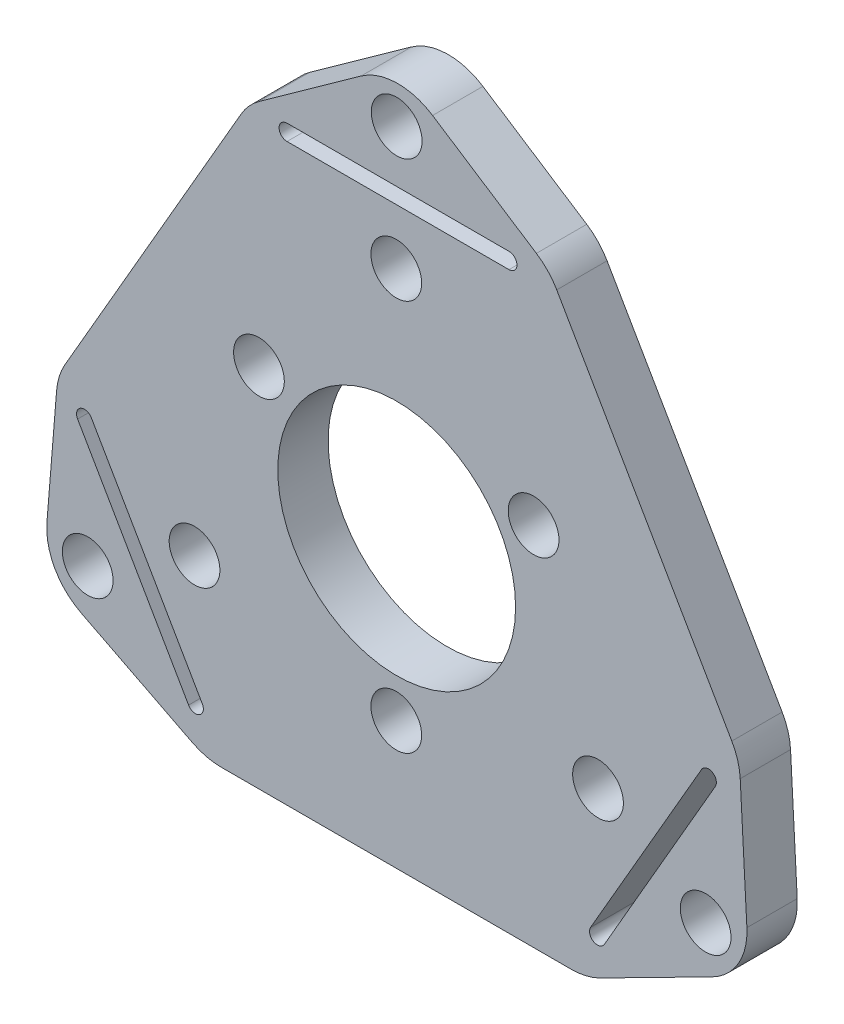
SolidWorks part; units mm, degrees
material "Acrylic (Medium-high impact)"
ref_plane "Front" through (0, 0, 0) normal (0, 0, 1) x (1, 0, 0)
ref_plane "Top" through (0, 0, 0) normal (0, 1, 0) x (1, 0, 0)
ref_plane "Right" through (0, 0, 0) normal (1, 0, 0) x (0, 0, -1)
sketch "Sketch1" plane through (0, 0, 0) normal (0, 0, 1) x (1, 0, 0)
  line L0 (31.8906, 32.2685) -> (22.25, 38.5381) construction
  line L1 (43.8906, 11.4838) -> (31.8906, 32.2685) construction
  line L2 (44.5, 0) -> (43.8906, 11.4838) construction
  line L3 (34.25, -5.2142) -> (44.5, 0) construction
  line L4 (10.25, -5.2142) -> (34.25, -5.2142) construction
  line L5 (0, 0) -> (10.25, -5.2142) construction
  line L6 (0.8998, 11.0585) -> (0, 0) construction
  line L7 (0.8998, 11.0585) -> (12.8998, 31.8431) construction
  line L8 (12.8998, 31.8431) -> (22.25, 38.5381) construction
  line L9 (31.0867, 32.7912) -> (24.5392, 37.0494)
  line L10 (43.4111, 12.3143) -> (32.3701, 31.438)
  line L11 (44.3621, 2.5977) -> (43.9414, 10.5263)
  line L12 (35.1047, -4.7794) -> (42.1814, -1.1795)
  line L13 (11.2089, -5.2142) -> (33.2911, -5.2142)
  line L14 (2.3907, -1.2162) -> (9.3953, -4.7794)
  line L15 (0.8268, 10.1619) -> (0.2175, 2.6734)
  line L16 (1.3496, 11.8375) -> (12.4674, 31.0942)
  line L17 (13.6028, 32.3465) -> (20.0297, 36.9484)
  line L18 (41.9378, 9.5622) -> (34.9378, -2.5622) construction
  line L19 (42.3708, 9.3122) -> (35.3708, -2.8122)
  line L20 (41.5048, 9.8122) -> (34.5048, -2.3122)
  line L21 (33.8665, 12.846) -> (28.0583, 22.9063) construction
  line L22 (28.0583, 2.7858) -> (33.8665, 12.846) construction
  line L23 (16.4417, 2.7858) -> (28.0583, 2.7858) construction
  line L24 (10.6335, 12.846) -> (16.4417, 2.7858) construction
  line L25 (16.4417, 22.9063) -> (10.6335, 12.846) construction
  line L26 (28.0583, 22.9063) -> (16.4417, 22.9063) construction
  line L27 (33.8665, 12.846) -> (28.0583, 22.9063) construction
  line L28 (28.0583, 2.7858) -> (33.8665, 12.846) construction
  line L29 (16.4417, 2.7858) -> (28.0583, 2.7858) construction
  line L30 (10.6335, 12.846) -> (16.4417, 2.7858) construction
  line L31 (16.4417, 22.9063) -> (10.6335, 12.846) construction
  line L32 (28.0583, 22.9063) -> (16.4417, 22.9063) construction
  line L33 (22.25, 12.846) -> (44.5, 0) construction
  line L34 (22.25, 12.846) -> (7.0114, 21.6441) construction
  line L37 (10.0175, -2.3499) -> (3.0175, 9.7744)
  line L40 (9.1515, -2.8499) -> (2.1515, 9.2744)
  line L41 (9.5845, -2.5999) -> (2.5845, 9.5244) construction
  line L42 (15.3585, 31.0381) -> (29.3585, 31.0381)
  line L43 (15.3585, 32.0381) -> (29.3585, 32.0381)
  line L44 (15.3585, 31.5381) -> (29.3585, 31.5381) construction
  line L45 (9.5263, 5.5) -> (4.2044, 2.3491) construction
  circle A0 centre (34.9737, 5.5) radius 1.5 construction
  arc A1 (9.1515, -2.8499) -> (10.0175, -2.3499) centre (9.5845, -2.5999) ccw
  arc A3 (3.0175, 9.7744) -> (2.1515, 9.2744) centre (2.5845, 9.5244) ccw
  arc A4 (15.3585, 32.0381) -> (15.3585, 31.0381) centre (15.3585, 31.5381) ccw
  arc A12 (31.0867, 32.7912) -> (32.3701, 31.438) centre (28.906, 29.438) cw
  arc A13 (43.4111, 12.3143) -> (43.9414, 10.5263) centre (39.947, 10.3143) cw
  arc A14 (44.3621, 2.5977) -> (42.1814, -1.1795) centre (40.3678, 2.3857) cw
  arc A15 (35.1047, -4.7794) -> (33.2911, -5.2142) centre (33.2911, -1.2142) cw
  arc A16 (11.2089, -5.2142) -> (9.3953, -4.7794) centre (11.2089, -1.2142) cw
  arc A17 (2.3907, -1.2162) -> (0.2175, 2.6734) centre (4.2044, 2.3491) cw
  arc A18 (0.8268, 10.1619) -> (1.3496, 11.8375) centre (4.8137, 9.8375) cw
  arc A19 (12.4674, 31.0942) -> (13.6028, 32.3465) centre (15.9315, 29.0942) cw
  arc A20 (24.5392, 37.0494) -> (20.0297, 36.9484) centre (22.3585, 33.6961) ccw
  arc A21 (42.3708, 9.3122) -> (41.5048, 9.8122) centre (41.9378, 9.5622) ccw
  arc A22 (34.5048, -2.3122) -> (35.3708, -2.8122) centre (34.9378, -2.5622) ccw
  circle A23 centre (22.25, 12.846) radius 10.0602 construction
  circle A24 centre (9.5263, 5.5) radius 1.6 construction
  circle A29 centre (34.9737, 5.5) radius 1.6 construction
  circle A31 centre (22.25, 27.5381) radius 1.6 construction
  circle A32 centre (13.5897, 17.846) radius 1.6
  circle A33 centre (9.5263, 5.5) radius 1.6
  circle A34 centre (34.9737, 5.5) radius 1.6
  circle A35 centre (30.9103, 17.846) radius 1.6
  circle A36 centre (22.25, 27.5381) radius 1.6
  circle A38 centre (22.25, 2.846) radius 1.6
  arc A39 (29.3585, 31.0381) -> (29.3585, 32.0381) centre (29.3585, 31.5381) ccw
  circle A40 centre (22.25, 12.846) radius 10 construction
  point P9 (0, 0)
  point P20 (0, 0)
  point P23 (0, 0)
  point P56 (38.4378, 3.5)
  point P74 (0, 0)
  point P76 (6.0845, 3.4622)
  point P85 (22.3585, 31.5381)
  point P90 (0, 0)
  dimension "D1" = 4
  dimension "D3" = 20
  dimension "D2" = 14
  dimension "D4" = 4
  dimension "D5" = 1
extrude "Boss-Extrude1" add sketch "Sketch1" along normal blind 3.175
sketch "Sketch2" plane through (0, 0, 3.175) normal (0, 0, 1) x (1, 0, 0)
  circle A0 centre (22.2755, 12.8138) radius 24.8824 construction
  circle A1 centre (41.761, 1.5638) radius 1.6
  arc A2 (24.5392, 37.0494) -> (20.0297, 36.9484) centre (22.3585, 33.6961) ccw construction
  arc A3 (42.1814, -1.1795) -> (44.3621, 2.5977) centre (40.3678, 2.3857) ccw construction
  circle A4 centre (2.7899, 1.5638) radius 1.6
  arc A6 (0.2175, 2.6734) -> (2.3907, -1.2162) centre (4.2044, 2.3491) ccw construction
  circle A7 centre (22.2755, 12.8138) radius 7.5
  circle A8 centre (22.2755, 35.3138) radius 1.6
  circle A9 centre (22.25, 27.5381) radius 1.6 construction
  dimension "D1" = 15
  dimension "D2" = 22.5
  dimension "D3" = 3
extrude "Cut-Extrude1" cut sketch "Sketch2" against normal through all
